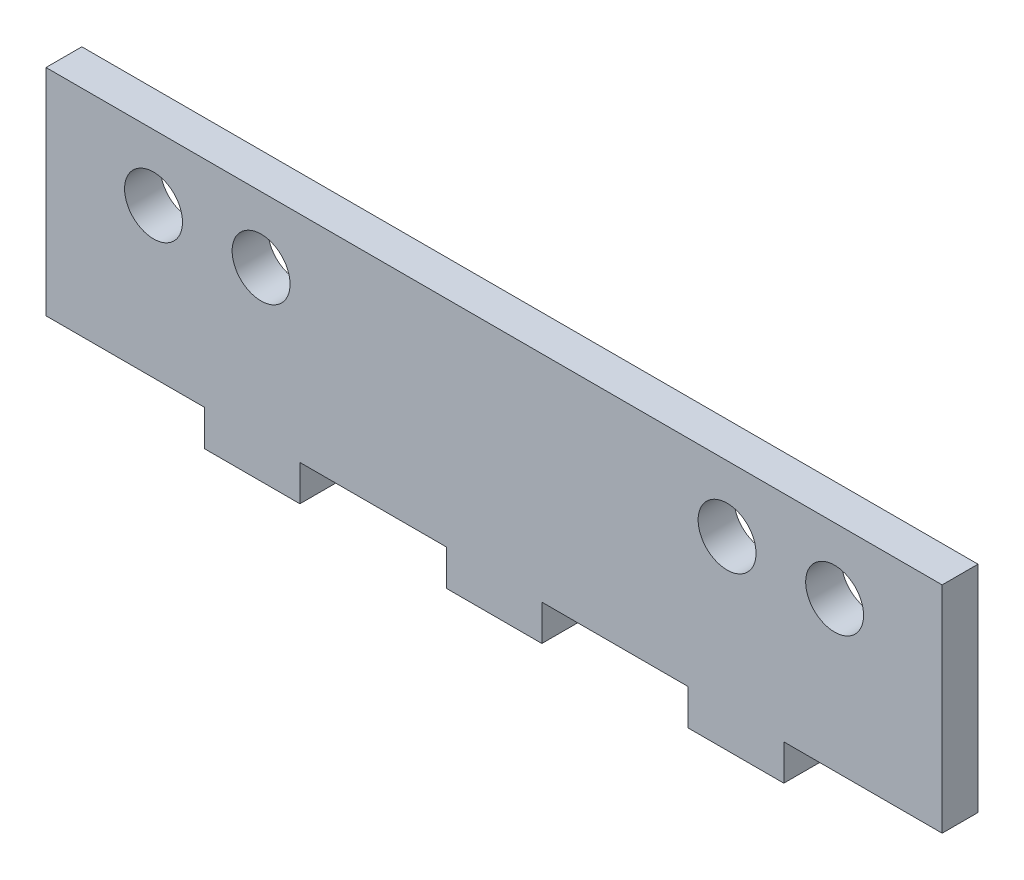
SolidWorks part; units mm, degrees
ref_plane "Front Plane" through (0, 0, 0) normal (0, 0, 1) x (1, 0, 0)
ref_plane "Top Plane" through (0, 0, 0) normal (0, 1, 0) x (1, 0, 0)
ref_plane "Right Plane" through (0, 0, 0) normal (1, 0, 0) x (0, 0, -1)
sketch "Sketch1" plane through (0, 0, 0) normal (0, 0, 1) x (1, 0, 0)
  line L1 (37.5, 9) -> (-37.5, 9)
  line L2 (37.5, 9) -> (37.5, -9)
  line L3 (37.5, -9) -> (-37.5, -9)
  line L4 (-37.5, 9) -> (-37.5, -9)
  point P0 (0, 0)
  dimension "D1" = 75
  dimension "D2" = 18
extrude "Boss-Extrude1" add sketch "Sketch1" along normal blind 3
sketch "Sketch2" plane through (0, -9, 0) normal (0, -1, 0) x (-1, 0, 0)
  line L0 (37.5, 0) -> (-37.5, 0) construction
  line L1 (-24.25, 0) -> (-16.25, 0)
  line L2 (-24.25, 0) -> (-24.25, -3)
  line L3 (-24.25, -3) -> (-16.25, -3)
  line L4 (-16.25, 0) -> (-16.25, -3)
  line L5 (37.5, -3) -> (-37.5, -3) construction
  line L6 (-37.5, -3) -> (-37.5, 0) construction
  line L7 (-4, 0) -> (4, 0)
  line L8 (-4, 0) -> (-4, -3)
  line L9 (-4, -3) -> (4, -3)
  line L10 (4, 0) -> (4, -3)
  line L11 (16.25, 0) -> (24.25, 0)
  line L12 (16.25, 0) -> (16.25, -3)
  line L13 (16.25, -3) -> (24.25, -3)
  line L14 (24.25, 0) -> (24.25, -3)
  line L15 (37.5, -3) -> (37.5, 0) construction
  dimension "D1" = 8
  dimension "D2" = 8
  dimension "D3" = 8
  dimension "D4" = 13.25
  dimension "D5" = 13.25
  dimension "D6" = 12.25
extrude "Boss-Extrude2" add sketch "Sketch2" along normal blind 3
sketch "Sketch3" plane through (0, 0, 0) normal (0, 0, -1) x (-1, 0, 0)
  line L0 (-37.5, -9) -> (-37.5, 9) construction
  line L1 (-37.5, 9) -> (37.5, 9) construction
  line L2 (37.5, 9) -> (37.5, -9) construction
  circle A0 centre (-28.5, 3.5) radius 2.425
  circle A1 centre (28.5, 3.5) radius 2.425
  circle A2 centre (-19.5, 3.5) radius 2.425
  circle A3 centre (19.5, 3.5) radius 2.425
  point P14 (0, 0)
  dimension "D1" = 4.85
  dimension "D4" = 4.85
  dimension "D6" = 4.85
  dimension "D7" = 4.85
  dimension "D2" = 9
  dimension "D3" = 5.5
  dimension "D5" = 9
  dimension "D8" = 18
  dimension "D9" = 18
extrude "Cut-Extrude1" cut sketch "Sketch3" against normal blind 3
